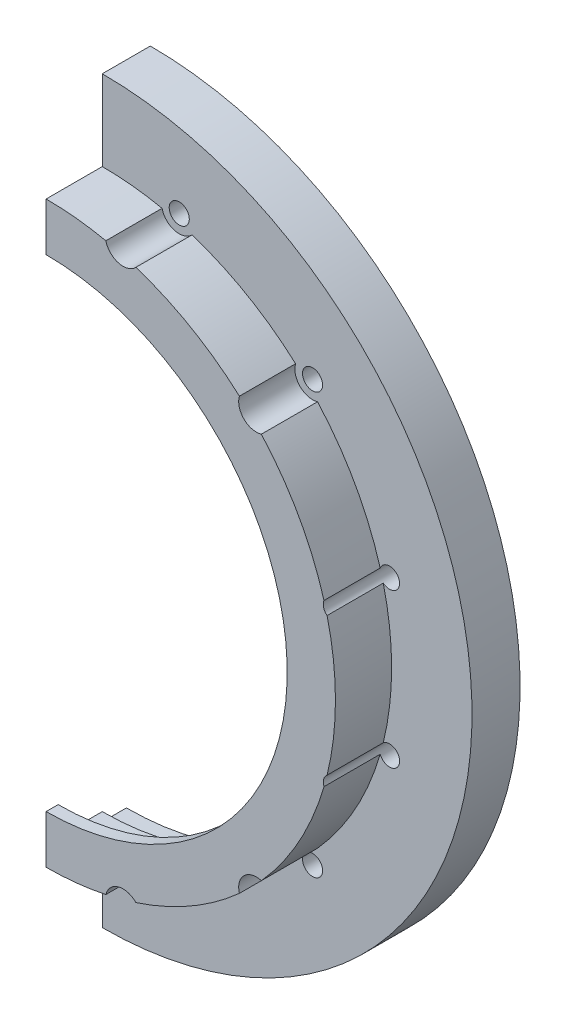
SolidWorks part; units mm, degrees
ref_plane "前视基准面" through (0, 0, 0) normal (0, 0, 1) x (1, 0, 0)
ref_plane "上视基准面" through (0, 0, 0) normal (0, 1, 0) x (1, 0, 0)
ref_plane "右视基准面" through (0, 0, 0) normal (1, 0, 0) x (0, 0, -1)
sketch "草图3" plane through (0, 0, 0) normal (0, 0, 1) x (1, 0, 0)
  circle A0 centre (0, 0) radius 34.6
  circle A1 centre (0, 0) radius 46
extrude "凸台-拉伸2" add sketch "草图3" along normal blind 3
ref_plane "基准面5" through (0, 0, 3) normal (0, 0, 1) x (1, 0, 0)
sketch "草图5" plane through (0, 0, 3) normal (0, 0, 1) x (1, 0, 0)
  circle A0 centre (0, 0) radius 33.5
  circle A1 centre (0, 0) radius 36
extrude "凸台-拉伸3" add sketch "草图5" along normal blind 5.49
sketch "草图2" plane through (0, 0, 0) normal (0, 0, 1) x (1, 0, 0)
  circle A0 centre (0, 0) radius 41.6
  circle A1 centre (0, 0) radius 46
extrude "凸台-拉伸1" add sketch "草图2" against normal blind 2.98
sketch "草图6" plane through (0, 0, 8.49) normal (0, 0, 1) x (1, 0, 0)
  circle A0 centre (0, 0) radius 30
  circle A1 centre (0, 0) radius 36
extrude "凸台-拉伸4" add sketch "草图6" along normal blind 1.5
sketch "草图8" plane through (0, 0, 0) normal (0, 0, 1) x (1, 0, 0)
  line L6 (-50, 20.008) -> (-45.0139, 20.008)
  line L8 (7.1335, 0) -> (-7.1335, 0) construction
  line L10 (-50, 20.008) -> (-50, -20.008)
  line L11 (-50, -20.008) -> (-45.0139, -20.008)
  arc A16 (-45.0139, 20.008) -> (-39.8396, 22.9958) centre (-45.0139, 25.9824) ccw
  arc A17 (-39.8396, 22.9958) -> (-39.8396, -22.9958) centre (0, 0) ccw
  arc A19 (-45.0139, -20.008) -> (-39.8396, -22.9958) centre (-45.0139, -25.9824) cw
extrude "凸台-拉伸5" add sketch "草图8" along normal blind 3 and the other way blind 2.98
hole_wizard "M3 螺纹孔的螺纹孔钻头1" positions "3D草图3" profile "草图12" hole size "M3" standard "ISO"
sketch3d "3D草图3"
  line L2 (0, 0, 0) -> (0, 37, 0)
  line L3 (0, 0, 0) -> (11.5811, 0, 0)
  point P55 (9.5763, 35.7393, 3)
  point P76 (26.163, 26.163, 3)
  point P83 (35.7393, 9.5763, 3)
  point P96 (-35.7393, 9.5763, 3)
  point P97 (-26.163, 26.163, 3)
  point P98 (-9.5763, 35.7393, 3)
  point P99 (35.7393, -9.5763, 3)
  point P100 (26.163, -26.163, 3)
  point P101 (9.5763, -35.7393, 3)
  point P102 (-9.5763, -35.7393, 3)
  point P103 (-26.163, -26.163, 3)
  point P104 (-35.7393, -9.5763, 3)
sketch "草图12" plane through (-35.7393, -9.5763, 3) normal (1, 0, 0) x (0, -1, 0)
  line L0 (0, 0) -> (0, 5.98)
  line L1 (0, 5.98) -> (1.25, 5.98)
  line L2 (1.25, 5.98) -> (1.25, 0)
  line L5 (1.25, 0) -> (0, 0)
  line L11 (0, -6.35) -> (0, 107.95) construction
  dimension "通孔孔直径" = 2.5
  dimension "通孔孔深度" = 5.98
sketch "草图13" plane through (0, 0, 3) normal (0, 0, 1) x (1, 0, 0)
  line L0 (0, 0) -> (0, 10.9464)
  line L1 (0, 0) -> (8.3109, 0)
  circle A0 centre (-35.7393, 9.5763) radius 1.25
  circle A1 centre (-26.163, 26.163) radius 2.2
  circle A2 centre (-9.5763, 35.7393) radius 2.2
  circle A3 centre (-9.5763, -35.7393) radius 2.2
  circle A4 centre (-26.163, -26.163) radius 2.2
  circle A5 centre (-35.7393, -9.5763) radius 1.25
  circle A6 centre (9.5763, -35.7393) radius 2.2
  circle A7 centre (26.163, -26.163) radius 2.2
  circle A8 centre (9.5763, 35.7393) radius 2.2
  circle A9 centre (26.163, 26.163) radius 2.2
  circle A10 centre (35.7393, -9.5763) radius 1.25
  circle A11 centre (35.7393, 9.5763) radius 1.25
extrude "切除-拉伸1" cut sketch "草图13" along normal up to next contours A5 | A4 | A0 | A1 | A2 | A9 | A11 | A10 | A6 | A3 | A8 | A7
sketch "草图25" plane through (0, 0, 3) normal (0, 0, 1) x (1, 0, 0)
  circle A0 centre (-9.5763, 35.7393) radius 3.25
  circle A1 centre (-26.163, 26.163) radius 3.25
  circle A2 centre (-35.7393, 9.5763) radius 3.25
  circle A3 centre (-35.7393, -9.5763) radius 3.25
  circle A4 centre (-26.163, -26.163) radius 3.25
  circle A5 centre (-9.5763, -35.7393) radius 3.25
extrude "切除-拉伸9" cut sketch "草图25" along normal blind 10
ref_plane "基准面6" through (-50, 0, 0) normal (-1, 0, 0) x (0, 0, 1)
sketch "草图26" plane through (-50, 0, 0) normal (-1, 0, 0) x (0, 0, 1)
  line L1 (-2.98, -20.008) -> (3, -20.008)
  line L5 (3, 20.008) -> (3, -20.008) construction
  line L6 (-2.98, 20.008) -> (3, 20.008)
  line L7 (3, 12.2277) -> (3, 23.2096) construction
  line L8 (3, 20.008) -> (3, -20.008)
  line L9 (-2.98, -20.008) -> (3, -20.008)
  arc A8 (-12.98, 26.5) -> (-12.98, -26.5) centre (-12.98, 0) ccw
  arc A9 (-12.98, 26.5) -> (-7.98, 23.254) centre (-12.98, 21.0261) cw
  arc A10 (-2.98, 20.008) -> (-7.98, 23.254) centre (-2.98, 25.4819) cw
  arc A11 (-2.98, -20.008) -> (-7.98, -23.254) centre (-2.98, -25.4819) ccw
  arc A12 (-12.98, -26.5) -> (-7.98, -23.254) centre (-12.98, -21.0261) ccw
extrude "凸台-拉伸7" add sketch "草图26" along normal blind 4 and the other way blind 2 contours A8 A12 A11 L1 L8 L6 A10 A9
fillet "圆角1" radius 5 1 edges at (-54, 0, 3)
sketch "草图27" plane through (0, 0, 0) normal (0, 0, 1) x (1, 0, 0)
  line L2 (0, 46) -> (0, -46)
  line L3 (0, -46) -> (-100, -46)
  line L4 (-100, -46) -> (-100, 46)
  line L5 (-100, 46) -> (0, 46)
  arc A2 (-39.8396, -22.9958) -> (-39.8396, 22.9958) centre (0, 0) ccw construction
extrude "切除-拉伸10" cut sketch "草图27" against normal through all both and the other way through all
